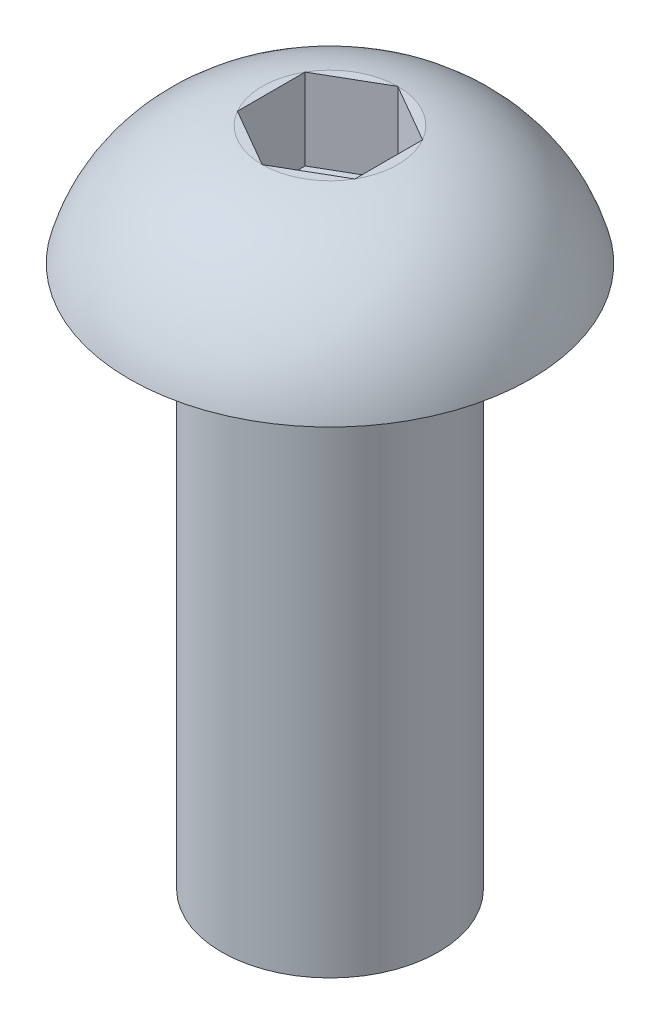
SolidWorks part; units mm, degrees
material "1023 Carbon Steel Sheet (SS)"
ref_plane "Front Plane" through (0, 0, 0) normal (0, 0, 1) x (1, 0, 0)
ref_plane "Top Plane" through (0, 0, 0) normal (0, 1, 0) x (1, 0, 0)
ref_plane "Right Plane" through (0, 0, 0) normal (1, 0, 0) x (0, 0, -1)
sketch "Sketch1" plane through (0, 0, 0) normal (1, 0, 0) x (0, 0, -1)
  line L2 (0, 0) -> (0, 2.2)
  line L3 (0, 2.2) -> (-1.25, 2.2)
  line L4 (0, 0) -> (-3.7, 0)
  line L5 (0, 4.7253) -> (0, -3.8299) construction
  arc A1 (-3.7, 0) -> (-1.25, 2.2) centre (-0.7994, -0.766) cw
  dimension "D2" = 1.25
  dimension "D4" = 2.2
  dimension "D3" = 3
  dimension "D1" = 3.7
revolve "Revolve1" add sketch "Sketch1" angle 360 about L5
sketch "Sketch2" plane through (0, 0, 0) normal (0, -1, 0) x (1, 0, 0)
  circle A0 centre (0, 0) radius 2
  dimension "D1" = 4
extrude "Boss-Extrude1" add sketch "Sketch2" along normal blind 10
sketch "Sketch3" plane through (0, 2.2, 0) normal (0, 1, 0) x (1, 0, 0)
  line L1 (0, 1.25) -> (-1.0825, 0.625)
  line L2 (-1.0825, 0.625) -> (-1.0825, -0.625)
  line L3 (-1.0825, -0.625) -> (0, -1.25)
  line L4 (0, -1.25) -> (1.0825, -0.625)
  line L5 (1.0825, -0.625) -> (1.0825, 0.625)
  line L6 (1.0825, 0.625) -> (0, 1.25)
  circle A0 centre (0, 0) radius 1.0825 construction
  dimension "D1" = 1.25
extrude "Cut-Extrude1" cut sketch "Sketch3" against normal blind 1.5
